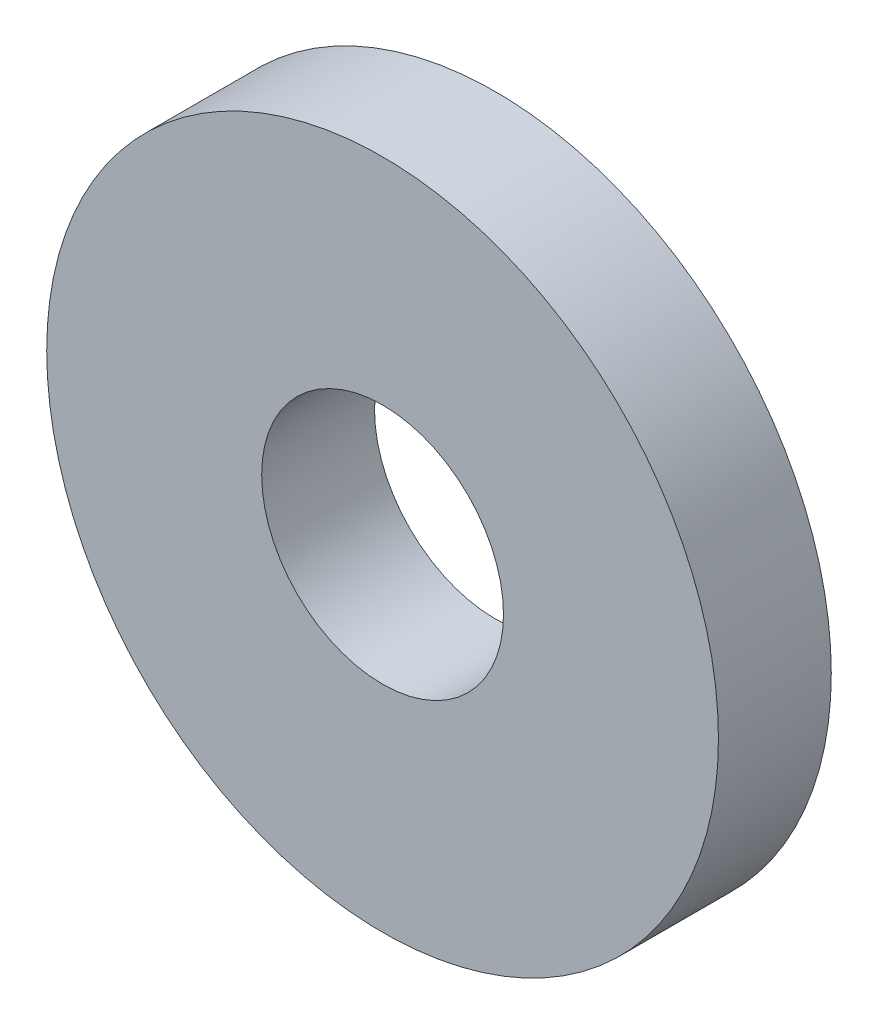
SolidWorks part; units mm, degrees
ref_plane "Front Plane" through (0, 0, 0) normal (0, 0, 1) x (1, 0, 0)
ref_plane "Top Plane" through (0, 0, 0) normal (0, 1, 0) x (1, 0, 0)
ref_plane "Right Plane" through (0, 0, 0) normal (1, 0, 0) x (0, 0, -1)
sketch "Sketch1" plane through (0, 0, 0) normal (0, 0, 1) x (1, 0, 0)
  circle A0 centre (0, 0) radius 9.525
  circle A1 centre (0, 0) radius 3.429
  dimension "D1" = 19.05
  dimension "D2" = 6.858
extrude "Boss-Extrude1" add sketch "Sketch1" along normal blind 3.2004
